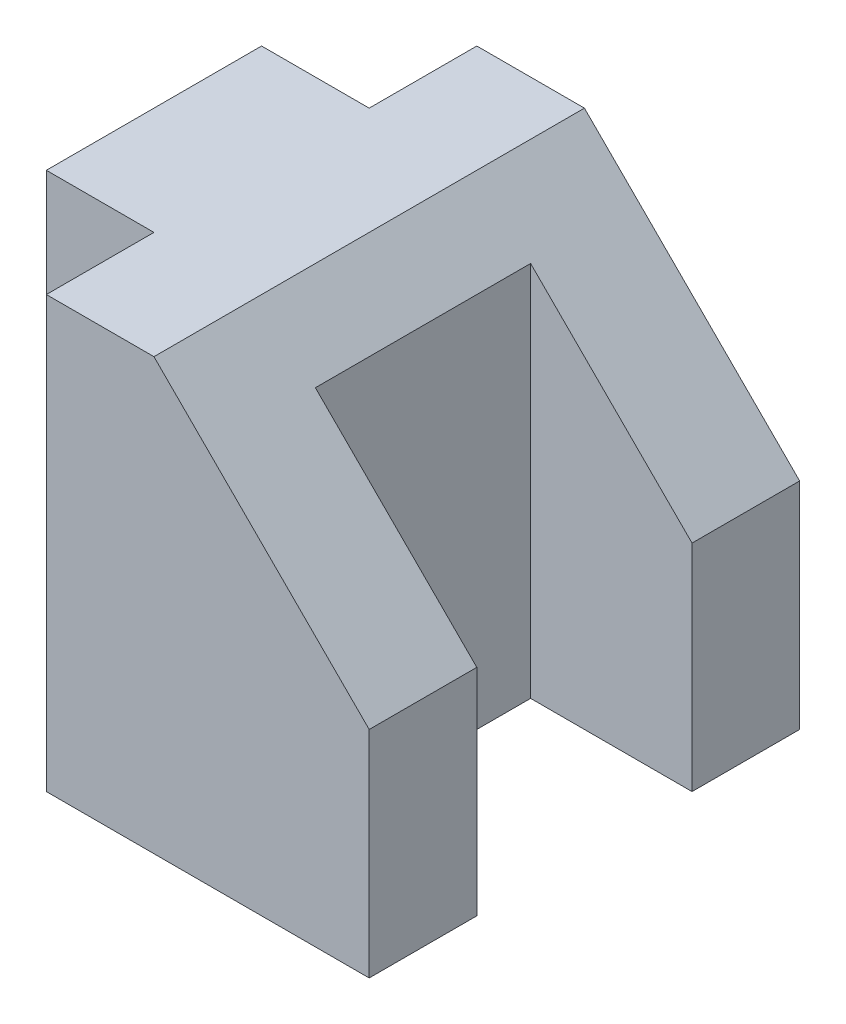
SolidWorks part; units mm, degrees
ref_plane "Front Plane" through (0, 0, 0) normal (0, 0, 1) x (1, 0, 0)
ref_plane "Top Plane" through (0, 0, 0) normal (0, 1, 0) x (1, 0, 0)
ref_plane "Right Plane" through (0, 0, 0) normal (1, 0, 0) x (0, 0, -1)
sketch "Sketch1" plane through (0, 0, 0) normal (0, 1, 0) x (1, 0, 0)
  line L0 (0, 0) -> (-38.1, 0)
  line L1 (-38.1, 0) -> (-38.1, 25.4)
  line L2 (-38.1, 25.4) -> (-63.5, 25.4)
  line L3 (-63.5, 25.4) -> (-63.5, 76.2)
  line L4 (-63.5, 76.2) -> (-38.1, 76.2)
  line L5 (-38.1, 76.2) -> (-38.1, 101.6)
  line L6 (-38.1, 101.6) -> (38.1, 101.6)
  line L7 (38.1, 101.6) -> (38.1, 76.2)
  line L8 (38.1, 76.2) -> (0, 76.2)
  line L9 (0, 76.2) -> (0, 25.4)
  line L10 (0, 25.4) -> (38.1, 25.4)
  line L11 (38.1, 25.4) -> (38.1, 0)
  line L12 (38.1, 0) -> (0, 0)
  point P14 (0, 0)
  point P15 (0, 0)
  point P16 (0, 0)
  dimension "D1" = 76.2
  dimension "D2" = 25.4
  dimension "D3" = 101.6
  dimension "D4" = 38.1
extrude "Boss-Extrude1" add sketch "Sketch1" along normal blind 101.6
sketch "Sketch2" plane through (0, 0, 0) normal (0, 0, 1) x (1, 0, 0)
  line L0 (38.1, 50.8) -> (-12.7, 50.8) construction
  line L1 (38.1, 101.6) -> (38.1, 0) construction
  line L2 (-12.7, 50.8) -> (-12.7, 101.6) construction
  line L3 (-12.7, 101.6) -> (38.1, 50.8)
  line L4 (-38.1, 101.6) -> (38.1, 101.6) construction
  line L5 (-12.7, 101.6) -> (38.1, 101.6)
  line L6 (38.1, 101.6) -> (38.1, 50.8)
  dimension "D1" = 50.8
  dimension "D2" = 50.8
extrude "Cut-Extrude2" cut sketch "Sketch2" against normal through all
